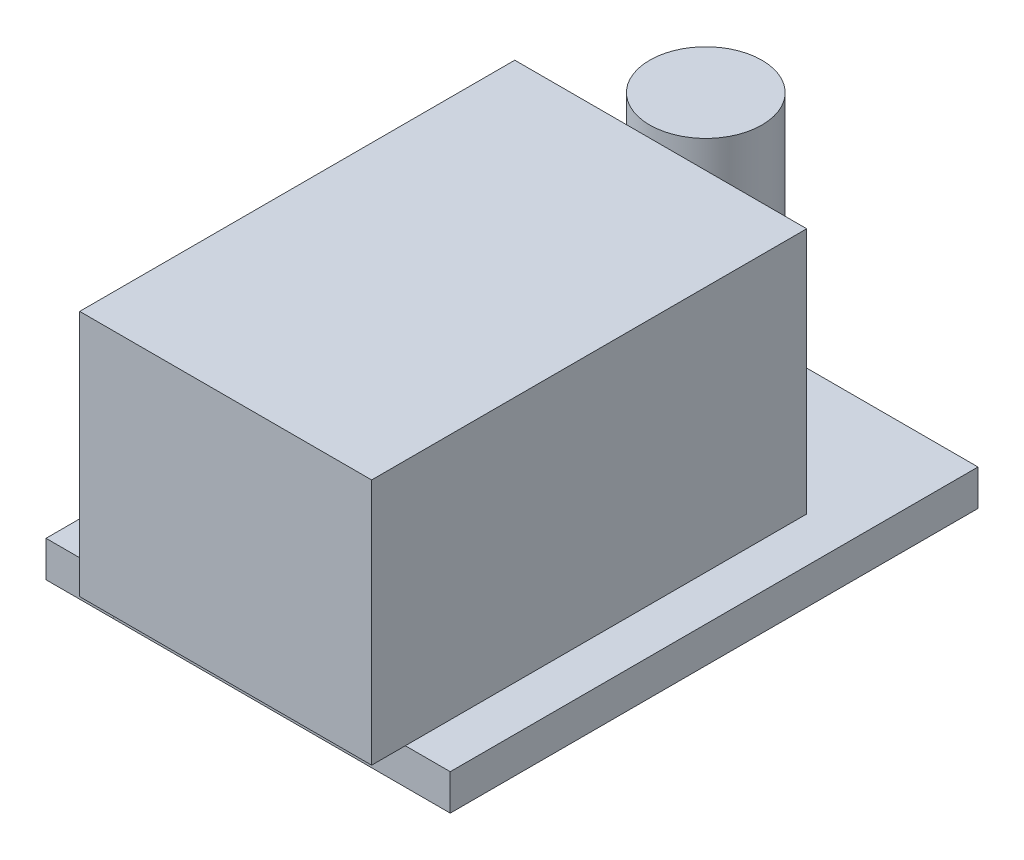
SolidWorks part; units mm, degrees
ref_plane "Front Plane" through (0, 0, 0) normal (0, 0, 1) x (1, 0, 0)
ref_plane "Top Plane" through (0, 0, 0) normal (0, 1, 0) x (1, 0, 0)
ref_plane "Right Plane" through (0, 0, 0) normal (1, 0, 0) x (0, 0, -1)
sketch "Sketch1" plane through (0, 0, 0) normal (0, 1, 0) x (1, 0, 0)
  line L1 (-7.5, -11.75) -> (7.5, -11.75)
  line L2 (-7.5, -11.75) -> (-7.5, 11.75)
  line L3 (-7.5, 11.75) -> (7.5, 11.75)
  line L4 (7.5, -11.75) -> (7.5, 11.75)
  point P4 (0, -11.75)
  point P6 (-7.5, 0)
  dimension "D1" = 15
  dimension "D2" = 23.5
extrude "Boss-Extrude1" add sketch "Sketch1" against normal blind 1.6
sketch "Sketch2" plane through (0, 0, 0) normal (0, 1, 0) x (1, 0, 0)
  line L0 (-7.5, 11.75) -> (-7.5, -11.75) construction
  line L1 (-7.5, 10.85) -> (-10.5, 10.85)
  line L2 (-7.5, 10.85) -> (-7.5, 6.35)
  line L3 (-7.5, 6.35) -> (-10.5, 6.35)
  line L4 (-10.5, 10.85) -> (-10.5, 6.35)
  line L5 (-7.5, -11.75) -> (7.5, -11.75) construction
  line L6 (-7.5, -4.25) -> (-10.5, -4.25)
  line L7 (-7.5, -4.25) -> (-7.5, -11.75)
  line L8 (-7.5, -11.75) -> (-10.5, -11.75)
  line L9 (-10.5, -4.25) -> (-10.5, -11.75)
  line L10 (7.5, 11.75) -> (-7.5, 11.75) construction
  dimension "D1" = 7.5
  dimension "D2" = 0.9
  dimension "D3" = 3
  dimension "D4" = 4.5
extrude "Boss-Extrude2" add sketch "Sketch2" against normal up to surface (1.6 mm away) separate body up to face at (0, -1.6, 0)
sketch "Sketch3" plane through (0, 0, 0) normal (0, 1, 0) x (1, 0, 0)
  line L0 (-7.5, 11.75) -> (-7.5, -11.75) construction
  line L1 (-7.5, -13.25) -> (5.5, -13.25)
  line L2 (-7.5, -13.25) -> (-7.5, 6.1236)
  line L3 (-7.5, 6.1236) -> (5.5, 6.1236)
  line L4 (5.5, -13.25) -> (5.5, 6.1236)
  line L5 (7.5, 11.75) -> (-7.5, 11.75) construction
  circle A0 centre (-1.9971, 9.1272) radius 2.5
  point P10 (-1.9971, 9.1272)
  dimension "D2" = 5
  dimension "D1" = 13
  dimension "D3" = 25
extrude "Boss-Extrude3" add sketch "Sketch3" along normal blind 11
